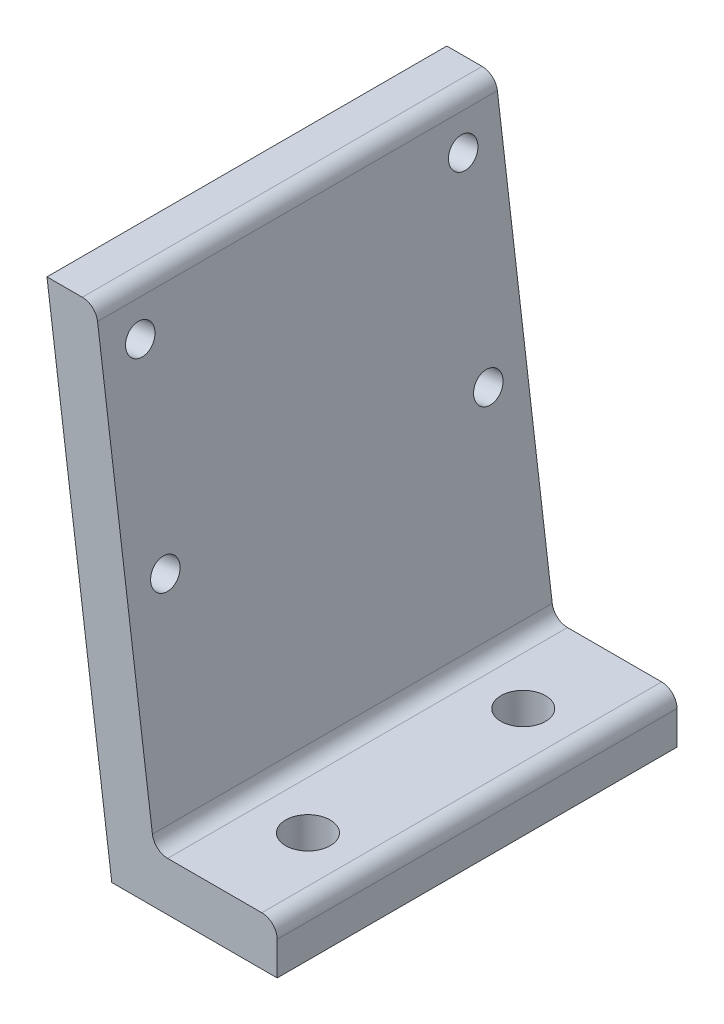
SolidWorks part; units mm, degrees
ref_plane "Front Plane" through (0, 0, 0) normal (0, 0, 1) x (1, 0, 0)
ref_plane "Top Plane" through (0, 0, 0) normal (0, 1, 0) x (1, 0, 0)
ref_plane "Right Plane" through (0, 0, 0) normal (1, 0, 0) x (0, 0, -1)
sketch "Sketch1" plane through (0, 0, 0) normal (0, 0, 1) x (1, 0, 0)
  line L6 (0, 0) -> (8, 0)
  line L7 (8, 0) -> (8, -3.175)
  line L14 (8, -3.175) -> (-2.757, -3.175)
  line L15 (-2.757, -3.175) -> (-6.9699, 28.825)
  line L16 (-6.9699, 28.825) -> (-3.7949, 28.825)
  line L17 (-3.7949, 28.825) -> (0, 0)
  dimension "D1" = 3.175
  dimension "D2" = 97.5
  dimension "D3" = 8
  dimension "D4" = 97.5
  dimension "D5" = 32
extrude "Boss-Extrude1" add sketch "Sketch1" along normal blind 26
sketch "Sketch2" plane through (0, 0, 0) normal (0.9914, 0.1305, 0) x (0, 0, -1)
  line L0 (-26, 29.0737) -> (0, 29.0737) construction
  line L1 (-13, 29.0737) -> (-13, 0) construction
  line L2 (-26, 0) -> (0, 0) construction
  line L4 (-23.5, 26.0737) -> (-2.5, 26.0737) construction
  line L5 (-23.5, 26.0737) -> (-23.5, 13.5737) construction
  line L6 (-23.5, 13.5737) -> (-2.5, 13.5737) construction
  line L7 (-2.5, 26.0737) -> (-2.5, 13.5737) construction
  line L8 (-23.5, 26.0737) -> (-2.5, 13.5737) construction
  line L9 (-23.5, 13.5737) -> (-2.5, 26.0737) construction
  circle A0 centre (-23.5, 26.0737) radius 0.95
  circle A1 centre (-2.5, 26.0737) radius 0.95
  circle A2 centre (-2.5, 13.5737) radius 0.95
  circle A3 centre (-23.5, 13.5737) radius 0.95
  point P0 (-13, 29.0737)
  point P7 (-13, 19.8237)
  dimension "D3" = 1.9
  dimension "D1" = 21
  dimension "D2" = 12.5
  dimension "D4" = 3
extrude "Cut-Extrude1" cut sketch "Sketch2" against normal up to surface (3.1478 mm away)
sketch "Sketch3" plane through (0, 0, 0) normal (0, 1, 0) x (1, 0, 0)
  line L0 (8, -26) -> (8, 0) construction
  line L1 (8, -13) -> (0, -13) construction
  line L2 (0, -26) -> (0, 0) construction
  circle A0 centre (4, -20) radius 1.45
  circle A1 centre (4, -6) radius 1.45
  dimension "D1" = 2.9
  dimension "D2" = 7
extrude "Cut-Extrude2" cut sketch "Sketch3" against normal up to surface (3.175 mm away) up to face at (2.6215, -3.175, 13)
fillet "Fillet1" radius 1 1 edges at (-3.7949, 28.825, 13)
fillet "Fillet2" radius 1 1 edges at (0, 0, 13)
fillet "Fillet3" radius 1 1 edges at (8, 0, 13)
equation "\"a\"= 105'Thanks Eric! <3"
